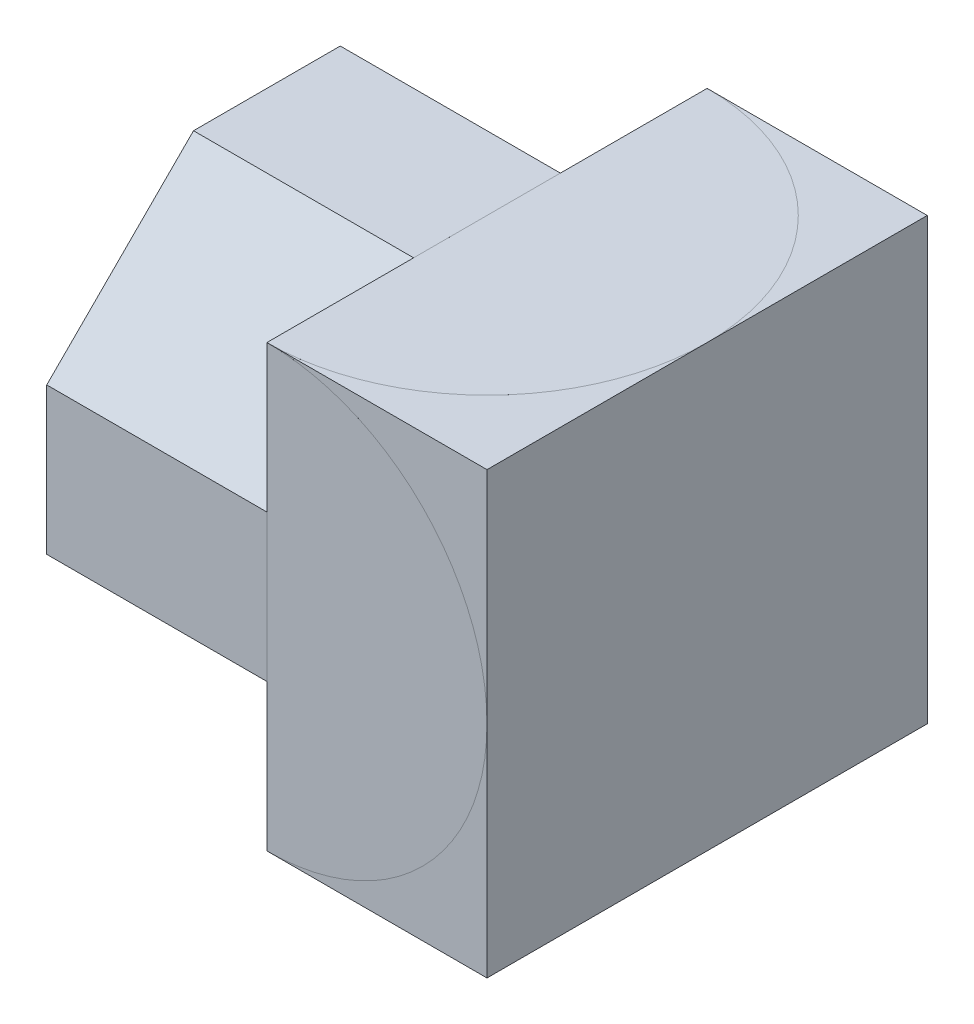
SolidWorks part; units mm, degrees
ref_plane "Front Plane" through (0, 0, 0) normal (0, 0, 1) x (1, 0, 0)
ref_plane "Top Plane" through (0, 0, 0) normal (0, 1, 0) x (1, 0, 0)
ref_plane "Right Plane" through (0, 0, 0) normal (1, 0, 0) x (0, 0, -1)
sketch "Sketch1" plane through (0, 0, 0) normal (0, 0, 1) x (1, 0, 0)
  line L1 (0, 0) -> (60, 0)
  line L2 (0, 0) -> (0, 60)
  line L3 (0, 60) -> (60, 60)
  line L4 (60, 0) -> (60, 60)
  dimension "D1" = 60
  dimension "D2" = 60
extrude "Boss-Extrude1" add sketch "Sketch1" along normal blind 60
sketch "Sketch3" plane through (0, 60, 0) normal (0, 1, 0) x (1, 0, 0)
  line L1 (0, 0) -> (30, 0)
  line L2 (0, 0) -> (0, -20)
  line L3 (0, -20) -> (30, -20)
  line L4 (30, 0) -> (30, -20)
  dimension "D1" = 30
  dimension "D2" = 20
extrude "Cut-Extrude1" cut sketch "Sketch3" against normal blind 20
sketch "Sketch4" plane through (0, 60, 0) normal (0, 1, 0) x (1, 0, 0)
  line L1 (0, -60) -> (30, -60)
  line L2 (0, -60) -> (0, -40)
  line L3 (0, -40) -> (30, -40)
  line L4 (30, -60) -> (30, -40)
  dimension "D1" = 20
  dimension "D2" = 30
extrude "Cut-Extrude2" cut sketch "Sketch4" against normal blind 20
sketch "Sketch5" plane through (0, 0, 0) normal (-1, 0, 0) x (0, 0, 1)
  line L0 (60, 40) -> (40, 60)
  line L1 (40, 60) -> (40, 40)
  line L2 (40, 40) -> (60, 40)
  line L3 (0, 40) -> (20, 40)
  line L4 (20, 40) -> (20, 60)
  line L5 (20, 60) -> (0, 40)
extrude "Boss-Extrude2" add sketch "Sketch5" against normal blind 30
sketch "Sketch6" plane through (0, 0, 0) normal (-1, 0, 0) x (0, 0, 1)
  line L0 (60, 20) -> (40, 0)
  line L1 (60, 40) -> (60, 0) construction
  line L2 (60, 0) -> (0, 0) construction
  line L3 (40, 0) -> (60, 0)
  line L4 (60, 0) -> (60, 20)
  dimension "D1" = 20
extrude "Cut-Extrude3" cut sketch "Sketch6" against normal blind 30
sketch "Sketch7" plane through (0, 0, 0) normal (-1, 0, 0) x (0, 0, 1)
  line L0 (0, 20) -> (20, 0)
  line L1 (0, 40) -> (0, 0) construction
  line L2 (40, 0) -> (0, 0) construction
  line L3 (20, 0) -> (0, 0)
  line L4 (0, 0) -> (0, 20)
  dimension "D1" = 20
extrude "Cut-Extrude4" cut sketch "Sketch7" against normal blind 30
sketch "Sketch8" plane through (0, 60, 0) normal (0, 1, 0) x (1, 0, 0)
  line L0 (30, -60) -> (30, 0)
  arc A0 (30, 0) -> (30, -60) centre (30, -30) cw
  dimension "D1" = 30
  dimension "D2" = 10
  dimension "D3" = 30
  dimension "D4" = 30
extrude "Cut-Extrude6" cut sketch "Sketch8" against normal blind 0.0001
sketch "Sketch9" plane through (0, 0, 60) normal (0, 0, 1) x (1, 0, 0)
  line L0 (30, 0) -> (30, 60)
  arc A0 (30, 60) -> (30, 0) centre (30, 30) cw
  dimension "D1" = 30
  dimension "D2" = 10
  dimension "D3" = 30
extrude "Cut-Extrude7" cut sketch "Sketch9" against normal blind 0.0001
